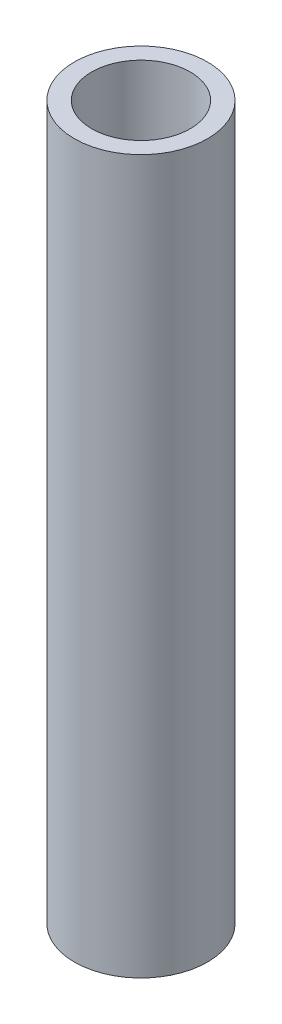
SolidWorks part; units mm, degrees
ref_plane "Front Plane" through (0, 0, 0) normal (0, 0, 1) x (1, 0, 0)
ref_plane "Top Plane" through (0, 0, 0) normal (0, 1, 0) x (1, 0, 0)
ref_plane "Right Plane" through (0, 0, 0) normal (1, 0, 0) x (0, 0, -1)
sketch "Sketch1" plane through (0, 0, 0) normal (0, 1, 0) x (1, 0, 0)
  circle A0 centre (0, 0) radius 7.8994
  circle A1 centre (0, 0) radius 10.668
  dimension "D1" = 21.336
  dimension "D2" = 15.7988
extrude "Boss-Extrude1" add sketch "Sketch1" along normal blind 114.3
